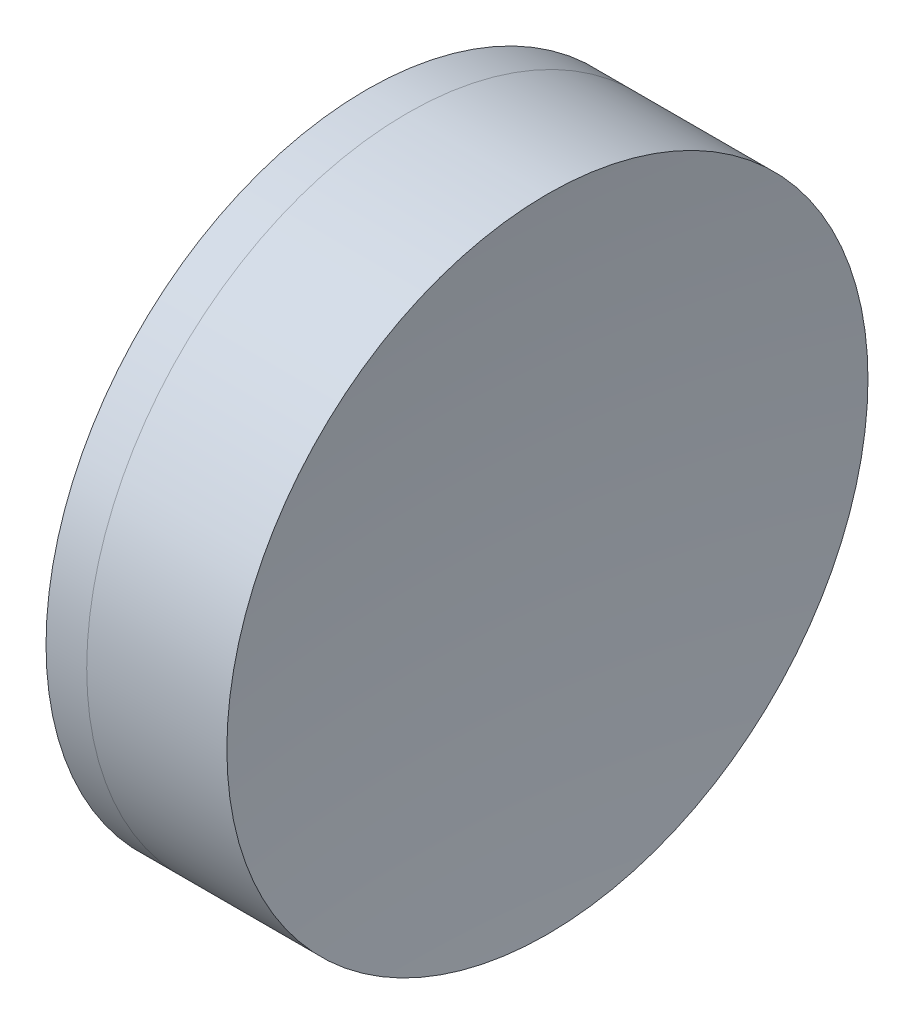
SolidWorks part; units mm, degrees
ref_plane "前视基准面" through (0, 0, 0) normal (0, 0, 1) x (1, 0, 0)
ref_plane "上视基准面" through (0, 0, 0) normal (0, 1, 0) x (1, 0, 0)
ref_plane "右视基准面" through (0, 0, 0) normal (1, 0, 0) x (0, 0, -1)
sketch "草图1" plane through (0, 0, 0) normal (0, 1, 0) x (1, 0, 0)
  line L0 (-0.8161, 0) -> (45.8933, 0) construction
  line L1 (36.8638, -12.7) -> (38.4753, -12.7)
  line L2 (36.8638, 12.7) -> (38.4753, 12.7)
  arc A0 (38.4753, -12.7) -> (38.4753, 12.7) centre (13.3866, 0) ccw
  arc A1 (36.8638, 12.7) -> (36.8638, -12.7) centre (57.0866, 0) ccw
  point P10 (33.2066, 0)
  point P11 (41.5066, 0)
  dimension "D3" = 23.88
  dimension "D4" = 28.12
  dimension "D1" = 12.7
  dimension "D2" = 12.7
  dimension "D5" = 8.3
revolve "旋转1" add sketch "草图1" angle 360 about L0
sketch "草图2" plane through (0, 0, 0) normal (0, 1, 0) x (1, 0, 0)
  line L0 (-0.5519, 0) -> (45.4982, 0) construction
  line L2 (38.4753, 12.7) -> (44.0285, 12.7)
  line L3 (38.4753, -12.7) -> (44.0285, -12.7)
  arc A0 (44.0285, 12.7) -> (44.0285, -12.7) centre (155.3866, 0) ccw
  arc A1 (38.4753, -12.7) -> (38.4753, 12.7) centre (13.3866, 0) ccw construction
  arc A2 (38.4753, -12.7) -> (38.4753, 12.7) centre (13.3866, 0) ccw
  point P4 (41.5066, 0)
  point P8 (43.3066, 0)
  dimension "D1" = 112.08
  dimension "D2" = 1.8
revolve "旋转2" add sketch "草图2" angle 360 about L0
